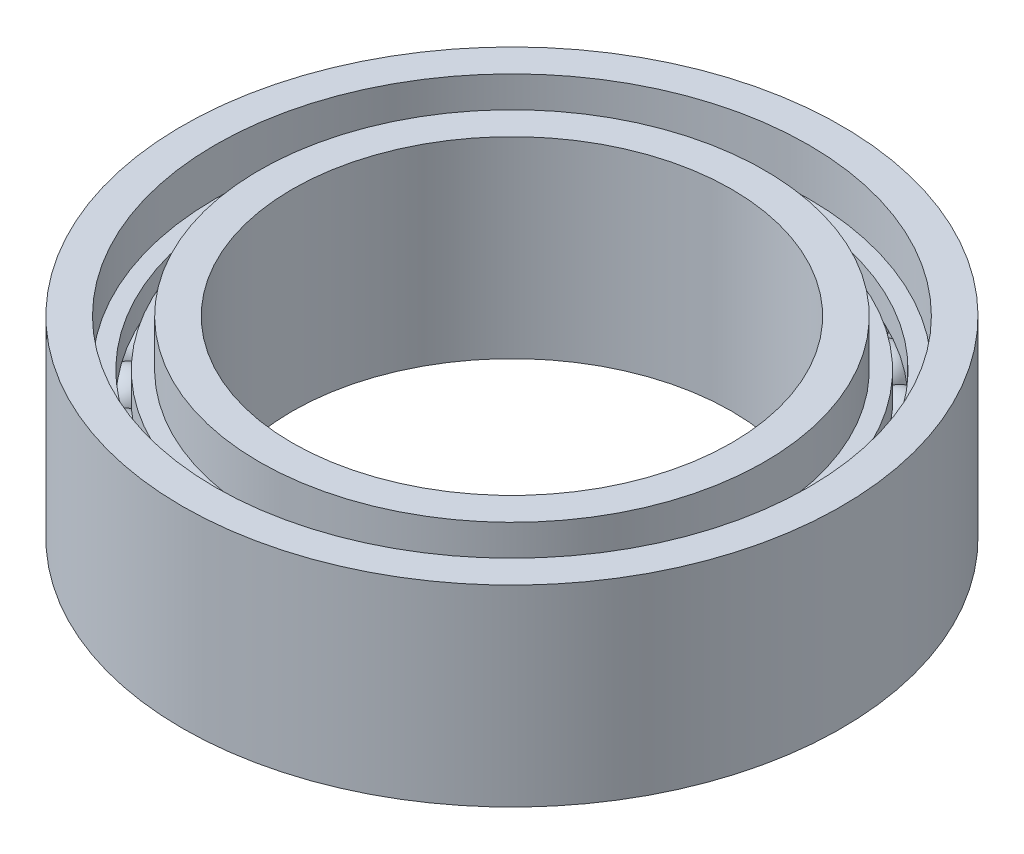
SolidWorks part; units mm, degrees
ref_plane "정면" through (0, 0, 0) normal (0, 0, 1) x (1, 0, 0)
ref_plane "윗면" through (0, 0, 0) normal (0, 1, 0) x (1, 0, 0)
ref_plane "우측면" through (0, 0, 0) normal (1, 0, 0) x (0, 0, -1)
sketch "스케치1" plane through (0, 0, 0) normal (0, 1, 0) x (1, 0, 0)
  circle A0 centre (0, 0) radius 4
  circle A1 centre (0, 0) radius 6
  circle A2 centre (0, 0) radius 4.6
  circle A3 centre (0, 0) radius 5.4
  dimension "D1" = 8
  dimension "D2" = 12
  dimension "D3" = 0.6
  dimension "D4" = 0.6
extrude "보스-돌출1" add sketch "스케치1" along normal blind 3.5 contours A1 A3 | A2 A0
ref_plane "평면1" through (0, 1.75, 0) normal (0, 1, 0) x (1, 0, 0)
sketch "스케치2" plane through (0, 1.75, 0) normal (0, 1, 0) x (1, 0, 0)
  line L0 (-55, 0) -> (55, 0) construction
  line L1 (-6.6376, 0) -> (6.8354, 0)
  circle A0 centre (-5, 0) radius 0.4
  circle A1 centre (0, 0) radius 4.6 construction
  circle A2 centre (0, 0) radius 4.6
  circle A3 centre (0, 0) radius 5.4 construction
  circle A4 centre (0, 0) radius 5.4
revolve "회전1" add sketch "스케치2" angle 360 about L1
pattern_circular "원형 패턴7" count 30 over 360 about axis through (0, 0, 0) along (0, 1, 0) of bodies 104
ref_plane "평면2" through (0, 2.15, 0) normal (0, 1, 0) x (1, 0, 0)
sketch "스케치4" plane through (0, 2.15, 0) normal (0, 1, 0) x (1, 0, 0)
  circle A0 centre (0, 0) radius 5.4 construction
  circle A2 centre (0, 0) radius 4.6 construction
  circle A11 centre (0, 0) radius 4.6
  circle A12 centre (0, 0) radius 5.4
  circle A13 centre (0, 0) radius 4.9
  circle A14 centre (0, 0) radius 5.1
  dimension "D1" = 0.5
  dimension "D2" = 0.5
extrude "보스-돌출2" add sketch "스케치4" along normal blind 0.5 contours A12 A13 | A14 A11
ref_plane "평면5" through (0, 1.35, 0) normal (0, -1, 0) x (-1, 0, 0)
sketch "스케치6" plane through (0, 1.35, 0) normal (0, -1, 0) x (-1, 0, 0)
  circle A0 centre (0, 0) radius 4.9 construction
  circle A1 centre (0, 0) radius 5.4 construction
  circle A2 centre (0, 0) radius 4.9
  circle A3 centre (0, 0) radius 5.4
  circle A4 centre (0, 0) radius 4.6 construction
  circle A5 centre (0, 0) radius 4.6
  circle A6 centre (0, 0) radius 5.1 construction
  circle A7 centre (0, 0) radius 5.1
extrude "보스-돌출4" add sketch "스케치6" along normal blind 0.5 contours A3 A7 | A2 A5
